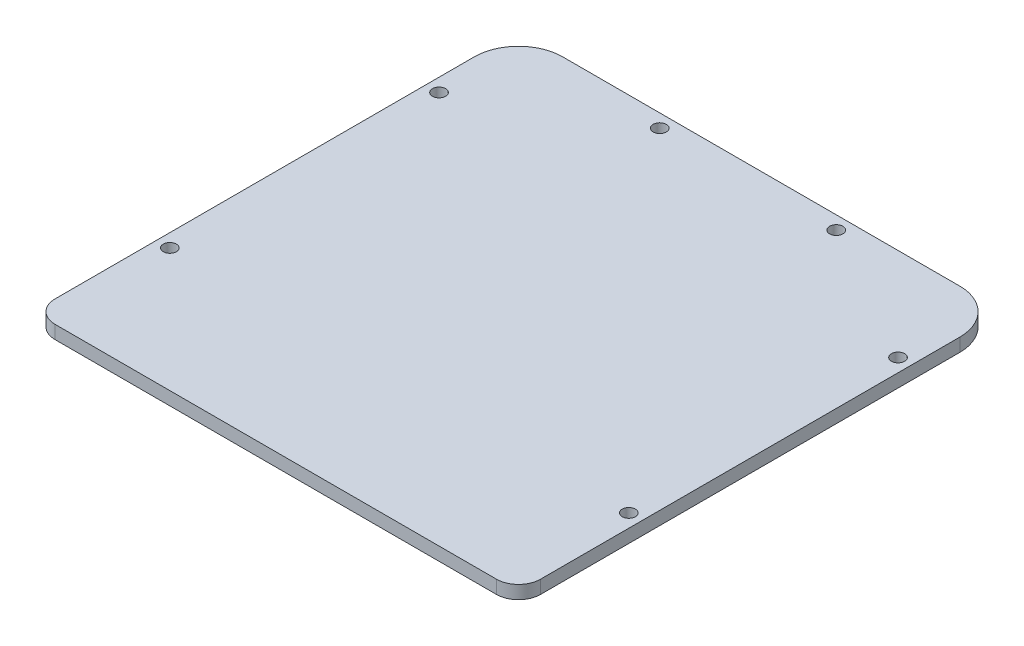
SolidWorks part; units mm, degrees
ref_plane "Front Plane" through (0, 0, 0) normal (0, 0, 1) x (1, 0, 0)
ref_plane "Top Plane" through (0, 0, 0) normal (0, 1, 0) x (1, 0, 0)
ref_plane "Right Plane" through (0, 0, 0) normal (1, 0, 0) x (0, 0, -1)
sketch "Sketch1" plane through (0, -220.6196, 0) normal (0, 1, 0) x (1, 0, 0)
  line L1 (-49.6351, 293.8303) -> (40.3649, 293.8303)
  line L2 (-59.6351, 283.8303) -> (-59.6351, 188.8303)
  line L3 (-54.6351, 183.8303) -> (45.3649, 183.8303)
  line L4 (50.3649, 283.8303) -> (50.3649, 188.8303)
  line L5 (-59.6351, 293.8303) -> (50.3649, 183.8303) construction
  line L6 (-59.6351, 183.8303) -> (50.3649, 293.8303) construction
  arc A0 (40.3649, 293.8303) -> (50.3649, 283.8303) centre (40.3649, 283.8303) cw
  arc A1 (-49.6351, 293.8303) -> (-59.6351, 283.8303) centre (-49.6351, 283.8303) ccw
  arc A2 (45.3649, 183.8303) -> (50.3649, 188.8303) centre (45.3649, 188.8303) ccw
  arc A3 (-59.6351, 188.8303) -> (-54.6351, 183.8303) centre (-54.6351, 188.8303) ccw
  point P0 (-4.6351, 238.8303)
  dimension "D3" = 10
  dimension "D4" = 5
  dimension "D1" = 110
  dimension "D2" = 110
extrude "Boss-Extrude1" add sketch "Sketch1" along normal blind 3
sketch "Sketch2" plane through (0, -217.6196, 0) normal (0, 1, 0) x (1, 0, 0)
  circle A0 centre (-24.6351, 290.8333) radius 1.5
  circle A1 centre (15.3649, 290.8333) radius 1.5
  circle A2 centre (47.3649, 272.8303) radius 1.5
  circle A3 centre (47.3649, 211.8303) radius 1.5
  circle A4 centre (-56.6351, 211.8303) radius 1.5 construction
  circle A5 centre (-56.6351, 211.8303) radius 1.5
  circle A6 centre (-56.6351, 272.8303) radius 1.5
  circle A8 centre (47.3649, 211.8303) radius 1.5 construction
  dimension "D1" = 0
  dimension "D2" = 3
  dimension "D3" = 3
  dimension "D4" = 0
  dimension "D5" = 3
  dimension "D6" = 3
  dimension "D7" = 3
extrude "Cut-Extrude1" cut sketch "Sketch2" against normal blind 3
